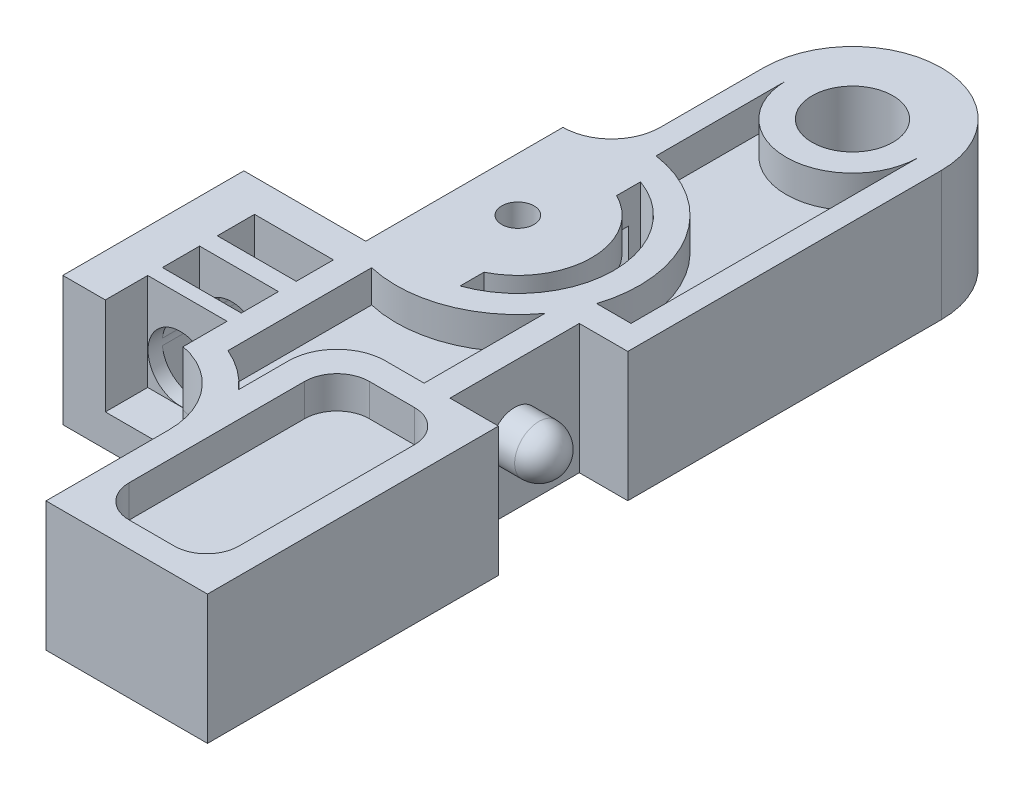
SolidWorks part; units mm, degrees
ref_plane "Front Plane" through (0, 0, 0) normal (0, 0, 1) x (1, 0, 0)
ref_plane "Top Plane" through (0, 0, 0) normal (0, 1, 0) x (1, 0, 0)
ref_plane "Right Plane" through (0, 0, 0) normal (1, 0, 0) x (0, 0, -1)
sketch "Sketch1" plane through (0, 0, 0) normal (0, 1, 0) x (1, 0, 0)
  line L1 (-21.56, 0) -> (-0.01, 0)
  line L2 (-21.56, 0) -> (-21.56, 50.9)
  line L3 (-21.56, 50.9) -> (-0.01, 50.9)
  line L4 (-0.01, 0) -> (-0.01, 50.9)
  dimension "D1" = 21.55
  dimension "D2" = 50.9
extrude "Boss-Extrude1" add sketch "Sketch1" along normal blind 8
sketch "Sketch2" plane through (0, 8, 0) normal (0, 1, 0) x (1, 0, 0)
  line L0 (-0.01, 0) -> (-0.01, 50.9) construction
  line L1 (-0.01, 50.9) -> (-21.56, 50.9) construction
  line L2 (-11.01, 45.4) -> (-11.01, 0) construction
  line L3 (-11.01, 39.0106) -> (-11.01, 45.4)
  line L4 (0, 0) -> (-0.01, 18)
  line L5 (-21.56, 0) -> (-0.01, 0) construction
  line L6 (4.9089, 18.5) -> (-33.8122, 18.5) construction
  line L7 (-37.2568, 26.1) -> (28.1891, 26.1) construction
  line L8 (-37.2568, 36) -> (-12.642, 36) construction
  line L9 (-14.0206, 36) -> (-14.0206, 23.8)
  line L10 (-14.0206, 23.8) -> (-21.56, 23.8)
  line L11 (-21.56, 50.9) -> (-21.56, 0) construction
  line L12 (-21.56, 23.8) -> (-21.56, 12.6)
  line L13 (-14.21, 36.006) -> (-14.21, 0) construction
  line L14 (-0.01, 45.4) -> (-0.01, 26)
  line L15 (-3.01, 26) -> (-3.01, 18)
  line L16 (-3.01, 22) -> (-7.4638, 22) construction
  line L17 (-0.01, 18) -> (-3.01, 18)
  line L18 (-0.01, 26) -> (-3.01, 26)
  line L19 (0, 0) -> (-10, 0)
  line L20 (-21.56, 12.6) -> (-10, 12.6)
  line L21 (-10, 12.6) -> (-10, 0)
  arc A0 (-0.01, 45.4) -> (-11.01, 45.4) centre (-5.51, 45.4) ccw
  arc A1 (-14.21, 36.006) -> (-11.01, 39.0106) centre (-14.0206, 39.0106) ccw
  dimension "D1" = 11
  dimension "D2" = 18
  dimension "D3" = 18.5
  dimension "D4" = 24.8
  dimension "D5" = 14.9
  dimension "D6" = 12.2
  dimension "D7" = 11.2
  dimension "D8" = 8
  dimension "D9" = 3
  dimension "D10" = 10
extrude "Cut-Extrude1" cut sketch "Sketch2" against normal blind 10
sketch "Sketch4" plane through (0, 8, 0) normal (0, 1, 0) x (1, 0, 0)
  line L0 (-17.8113, 29.9) -> (-3.6087, 29.9) construction
  line L1 (-0.01, 26) -> (-0.01, 45.4) construction
  circle A0 centre (-10.71, 29.9) radius 1
  dimension "D1" = 2
  dimension "D2" = 10.7
extrude "Cut-Extrude2" cut sketch "Sketch4" against normal blind 10
sketch "Sketch5" plane through (0, 8, 0) normal (0, 1, 0) x (1, 0, 0)
  circle A0 centre (-10.71, 29.9) radius 5.25
  dimension "D1" = 10.5
extrude "Cut-Extrude3" cut sketch "Sketch5" against normal blind 4 from offset 2 offset against normal yes
sketch "Sketch6" plane through (0, 8, 0) normal (0, 1, 0) x (1, 0, 0)
  line L0 (-8.7036, 35.4826) -> (-8.7036, 33.9999)
  line L1 (-8.7036, 25.8001) -> (-8.7036, 24.3174)
  arc A0 (-8.7036, 25.8001) -> (-8.7036, 33.9999) centre (-10.71, 29.9) ccw
  arc A1 (-8.7036, 24.3174) -> (-8.7036, 35.4826) centre (-10.71, 29.9) ccw
extrude "Cut-Extrude4" cut sketch "Sketch6" against normal blind 8
sketch "Sketch7" plane through (0, 8, 0) normal (0, 1, 0) x (1, 0, 0)
  circle A0 centre (-5.51, 45.4) radius 2.5
  dimension "D1" = 5
extrude "Cut-Extrude5" cut sketch "Sketch7" against normal blind 8
sketch "Sketch8" plane through (-3.01, 0, 0) normal (1, 0, 0) x (0, 0, -1)
  circle A0 centre (22, 4) radius 1.5
  dimension "D1" = 3
extrude "Boss-Extrude2" add sketch "Sketch8" along normal up to surface (3 mm away) up to face at (-0.01, 4, -35.7)
fillet "Fillet1" radius 1.5 1 edges at (-0.01, 4, -20.5)
sketch "Sketch9" plane through (0, 0, -12.6) normal (0, 0, 1) x (1, 0, 0)
  line L0 (-18.91, 4.0136) -> (-18.91, 7.1253) construction
  line L1 (-21.56, 0) -> (-21.56, 8) construction
  circle A0 centre (-16.91, 4.0136) radius 2
  dimension "D1" = 4
  dimension "D2" = 2.65
extrude "Cut-Extrude6" cut sketch "Sketch9" against normal up to next
fillet "Fillet2" radius 5 1 edges at (-10, 4, -12.6)
sketch "Sketch10" plane through (0, 8, 0) normal (0, 1, 0) x (1, 0, 0)
  line L0 (-21.56, 23.8) -> (-14.0206, 23.8) construction
  line L1 (-18.9, 21.8) -> (-14.0206, 21.8)
  line L2 (-18.9, 21.8) -> (-18.9, 19.5)
  line L3 (-18.9, 19.5) -> (-14.0206, 19.5)
  line L4 (-14.0206, 21.8) -> (-14.0206, 19.5)
  line L5 (-21.56, 23.8) -> (-21.56, 12.6) construction
  line L6 (-14.0206, 36) -> (-14.0206, 23.8) construction
  line L7 (-18.9, 18.4) -> (-14.0206, 18.4)
  line L8 (-18.9, 18.4) -> (-18.9, 16.1)
  line L9 (-18.9, 16.1) -> (-14.0206, 16.1)
  line L10 (-14.0206, 18.4) -> (-14.0206, 16.1)
  point P4 (-17.7903, 23.8)
  dimension "D1" = 2
  dimension "D2" = 2.66
  dimension "D3" = 2.3
  dimension "D4" = 2.3
  dimension "D5" = 1.1
extrude "Cut-Extrude7" cut sketch "Sketch10" against normal blind 8
sketch "Sketch11" plane through (0, 8, 0) normal (0, 1, 0) x (1, 0, 0)
  line L1 (-18.929, 15.2204) -> (-14.0206, 15.2204)
  line L2 (-18.929, 15.2204) -> (-18.929, 12.5031)
  line L3 (-18.929, 12.5031) -> (-14.0206, 12.5031)
  line L4 (-14.0206, 15.2204) -> (-14.0206, 12.5031)
  arc A0 (-10, 7.6) -> (-15, 12.6) centre (-15, 7.6) ccw construction
extrude "Cut-Extrude8" cut sketch "Sketch11" against normal blind 6
sketch "Sketch12" plane through (0, 8, 0) normal (0, 1, 0) x (1, 0, 0)
  line L0 (-9.61, 45.4) -> (-9.61, 37.3515)
  line L1 (-1.41, 45.4) -> (-1.41, 27.6)
  line L2 (-1.41, 27.6) -> (-3.5375, 27.6)
  line L3 (-0.01, 26) -> (-3.01, 26) construction
  arc A0 (-9.61, 45.4) -> (-1.41, 45.4) centre (-5.51, 45.4) ccw
  arc A1 (-3.5375, 27.6) -> (-9.61, 37.3515) centre (-10.71, 29.9) ccw
  arc A2 (-8.7036, 24.3174) -> (-8.7036, 35.4826) centre (-10.71, 29.9) ccw construction
  circle A3 centre (-5.51, 45.4) radius 2.5 construction
  dimension "D1" = 1.6
  dimension "D2" = 1.6
  dimension "D3" = 1.6
extrude "Cut-Extrude9" cut sketch "Sketch12" against normal blind 2
sketch "Sketch13" plane through (0, 0, 0) normal (0, -1, 0) x (1, 0, 0)
  line L0 (-3.5375, -27.6) -> (-1.41, -27.6)
  line L1 (-1.41, -27.6) -> (-1.41, -45.4)
  line L2 (-9.61, -37.3515) -> (-9.61, -45.4)
  circle A0 centre (-5.51, -45.4) radius 4.1
  arc A1 (-9.61, -37.3515) -> (-3.5375, -27.6) centre (-10.71, -29.9) ccw
extrude "Cut-Extrude11" cut sketch "Sketch13" against normal blind 2 contours A1 L2 A0 L1 L0
sketch "Sketch14" plane through (0, 8, 0) normal (0, 1, 0) x (1, 0, 0)
  line L0 (-12.4206, 22.5646) -> (-12.4206, 13.6751)
  line L1 (-4.61, 25.4813) -> (-4.61, 18)
  line L2 (-3.01, 26) -> (-3.01, 18) construction
  line L3 (-14.0206, 16.1) -> (-14.0206, 18.4) construction
  line L4 (-0.01, 0) -> (-0.01, 18) construction
  line L5 (-6.4, 16.4) -> (-3.61, 16.4)
  line L6 (-8.4, 14.4) -> (-8.4, 1.5468)
  line L7 (-8.4, 1.5468) -> (-1.61, 1.5468)
  line L8 (-1.61, 14.4) -> (-1.61, 1.5468)
  line L10 (-10, 7.6) -> (-10, 0) construction
  line L11 (-0.01, 18) -> (-3.01, 18) construction
  line L12 (-4.61, 18) -> (-10, 18)
  line L13 (-10, 18) -> (-10, 11.9081)
  arc A0 (-12.4206, 22.5646) -> (-4.61, 25.4813) centre (-10.71, 29.9) ccw
  arc A1 (-3.5375, 27.6) -> (-9.61, 37.3515) centre (-10.71, 29.9) ccw construction
  arc A2 (-10, 11.9081) -> (-12.4206, 13.6751) centre (-15, 7.6) ccw
  arc A3 (-10, 7.6) -> (-14.0206, 12.5031) centre (-15, 7.6) ccw construction
  arc A4 (-3.61, 16.4) -> (-1.61, 14.4) centre (-3.61, 14.4) cw
  arc A5 (-6.4, 16.4) -> (-8.4, 14.4) centre (-6.4, 14.4) ccw
  point P12 (-14.0206, 17.25)
  dimension "D3" = 1.6
  dimension "D7" = 2
  dimension "D1" = 1.6
  dimension "D2" = 1.6
  dimension "D4" = 1.6
  dimension "D5" = 1.6
  dimension "D6" = 1.6
  dimension "D8" = 1.6
  dimension "D9" = 1.6
extrude "Cut-Extrude12" cut sketch "Sketch14" against normal blind 2
fillet "Fillet3" radius 3 1 edges at (-10, 7, -18)
fillet "Fillet4" radius 2 2 edges at (-8.4, 7, -1.5468) (-1.61, 7, -1.5468)
sketch "Sketch15" plane through (0, 0, 0) normal (0, -1, 0) x (-1, 0, 0)
  line L0 (1.61, 3.5468) -> (1.61, 14.4) construction
  line L1 (6.4, 1.5468) -> (3.61, 1.5468)
  line L2 (8.4, 3.5468) -> (8.4, 14.4)
  line L3 (6.4, 16.4) -> (3.61, 16.4)
  line L4 (1.61, 3.5468) -> (1.61, 14.4)
  line L5 (6.4, 1.5468) -> (3.61, 1.5468) construction
  line L6 (4.61, 18) -> (4.61, 25.4813)
  line L7 (12.4206, 13.6751) -> (12.4206, 22.5646)
  line L8 (4.61, 18) -> (7, 18)
  line L9 (10, 11.9081) -> (10, 15)
  arc A1 (4.61, 25.4813) -> (12.4206, 22.5646) centre (10.71, 29.9) ccw
  arc A2 (12.4206, 13.6751) -> (10, 11.9081) centre (15, 7.6) ccw
  arc A3 (8.4, 14.4) -> (6.4, 16.4) centre (6.4, 14.4) ccw
  arc A4 (3.61, 16.4) -> (1.61, 14.4) centre (3.61, 14.4) ccw
  arc A5 (3.61, 1.5468) -> (1.61, 3.5468) centre (3.61, 3.5468) cw
  arc A6 (6.4, 1.5468) -> (8.4, 3.5468) centre (6.4, 3.5468) ccw
  arc A7 (7, 18) -> (10, 15) centre (7, 15) cw
  point P30 (1.61, 1.5468)
  dimension "D1" = 2
  dimension "D2" = 3
extrude "Cut-Extrude13" cut sketch "Sketch15" against normal blind 2 contours L4 L1 L2 L3 | A2 L7 A1 L6 L8 L9
sketch "Sketch16" plane through (-21.56, 0, 0) normal (-1, 0, 0) x (0, 0, 1)
  line L0 (-23.8, 0) -> (-23.8, 8) construction
  line L1 (-23.8, 5.5) -> (-21.8, 5.5)
  line L2 (-23.8, 5.5) -> (-23.8, 2.5)
  line L3 (-23.8, 2.5) -> (-21.8, 2.5)
  line L4 (-21.8, 5.5) -> (-21.8, 2.5)
  line L7 (-23.8, 0) -> (-12.6, 0) construction
  line L8 (-22.3678, 8) -> (-25.4813, 8) construction
  point P8 (-23.9245, 8)
  dimension "D1" = 2
  dimension "D2" = 3
  dimension "D3" = 2.5
extrude "Cut-Extrude14" cut sketch "Sketch16" against normal blind 7
sketch "Sketch17" plane through (0, 0, -23.8) normal (0, 0, -1) x (-1, 0, 0)
  line L0 (15.6028, 2.5) -> (18.2172, 2.5)
  line L1 (15.5718, 5.5) -> (18.2482, 5.5)
  arc A0 (15.6028, 2.5) -> (18.2172, 2.5) centre (16.91, 4.0136) ccw
  arc A1 (18.2482, 5.5) -> (15.5718, 5.5) centre (16.91, 4.0136) ccw
extrude "Boss-Extrude3" add sketch "Sketch17" against normal up to surface (2 mm away) up to face at (-16.7001, 4.0023, -21.8)
